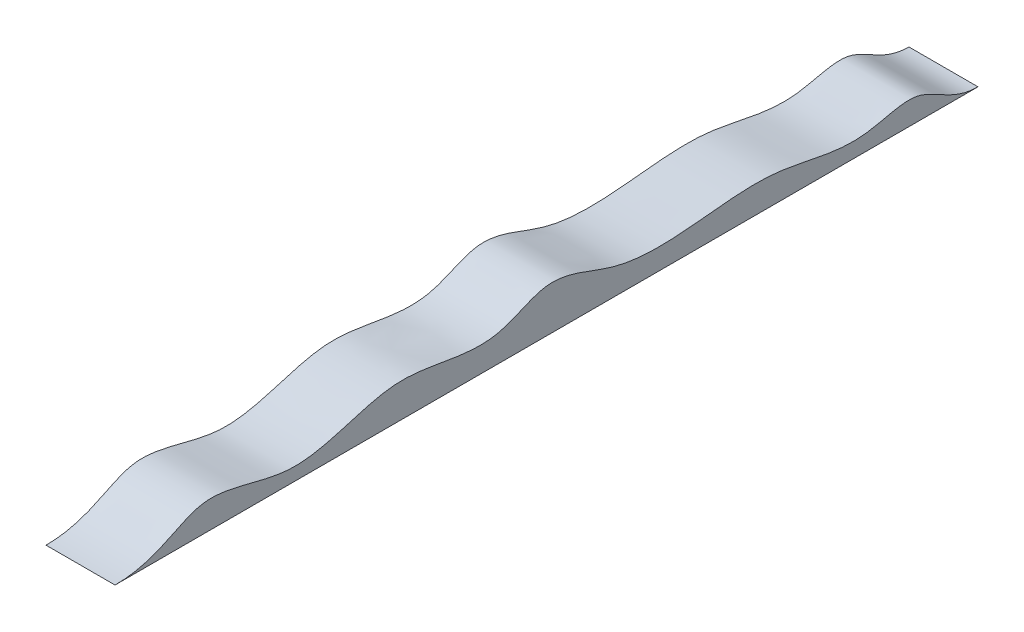
SolidWorks part; units mm, degrees
ref_plane "前视基准面" through (0, 0, 0) normal (0, 0, 1) x (1, 0, 0)
ref_plane "上视基准面" through (0, 0, 0) normal (0, 1, 0) x (1, 0, 0)
ref_plane "右视基准面" through (0, 0, 0) normal (1, 0, 0) x (0, 0, -1)
other "Configuration Table"
sketch "草图1" plane through (0, 0, 0) normal (1, 0, 0) x (0, 0, -1)
  line L0 (0, 0) -> (2000, 0)
  line L1 (1000, 0) -> (1000, 100) construction
  spline S0 degree 3 poles (0, 0) (103.7088, 0) (187.7892, 107.255) (431.9509, -12.1712) (648.4834, 121.0783) (857.9656, 26.116) (1013.58, 126.6123) (1150.2026, 48.699) (1329.4439, 45.2602) (1528.5775, 82.0456) (1707.183, 13.1473) (1874.7936, 78.6315) (1936.7681, 0) (2000, 0) knots 0 0 0 0 0.107407 0.205784 0.330572 0.447841 0.501425 0.5778 0.65357 0.76515 0.868833 0.924237 1 1 1 1
  point P6 (407.9962, 30.012)
  point P8 (1854.6184, 52.4002)
  dimension "D1" = 2000
  dimension "D2" = 100
extrude "凸台-拉伸1" add sketch "草图1" along normal mid plane 160
